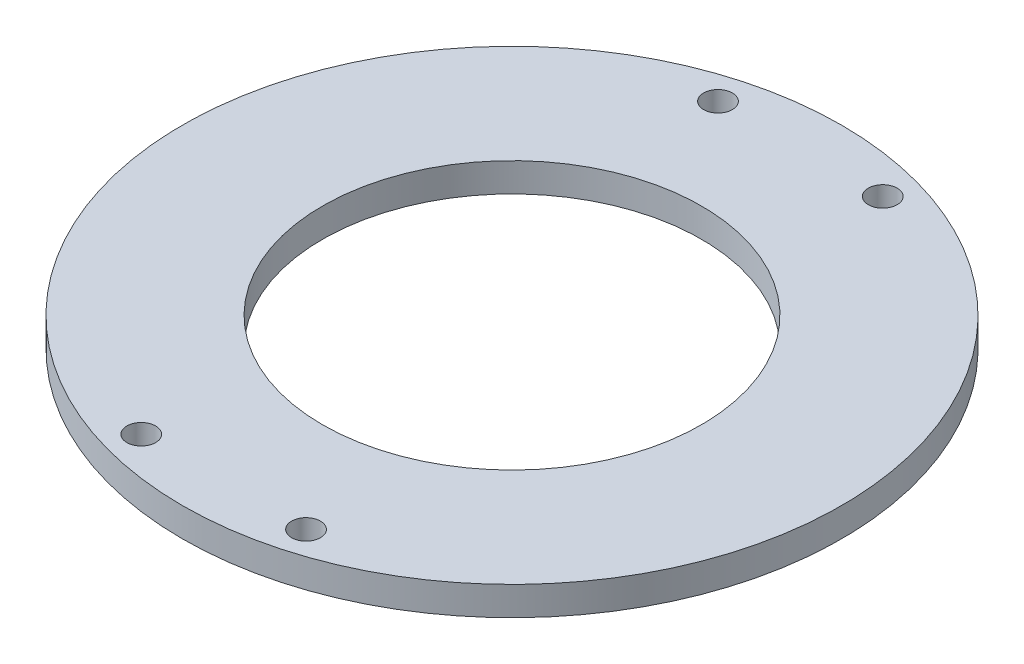
SolidWorks part; units mm, degrees
ref_plane "Front Plane" through (0, 0, 0) normal (0, 0, 1) x (1, 0, 0)
ref_plane "Top Plane" through (0, 0, 0) normal (0, 1, 0) x (1, 0, 0)
ref_plane "Right Plane" through (0, 0, 0) normal (1, 0, 0) x (0, 0, -1)
sketch "Sketch1" plane through (0, 0, 0) normal (0, 1, 0) x (1, 0, 0)
  circle A0 centre (0, 0) radius 40
  circle A1 centre (10, 35) radius 1.75
  circle A2 centre (-10, 35) radius 1.75
  circle A3 centre (10, -35) radius 1.75
  circle A4 centre (-10, -35) radius 1.75
  circle A5 centre (0, 0) radius 23
  dimension "D1" = 80
  dimension "D6" = 3.5
  dimension "D7" = 46
  dimension "D2" = 20
  dimension "D3" = 10
  dimension "D4" = 35
  dimension "D5" = 35
extrude "Boss-Extrude1" add sketch "Sketch1" along normal blind 3.5
